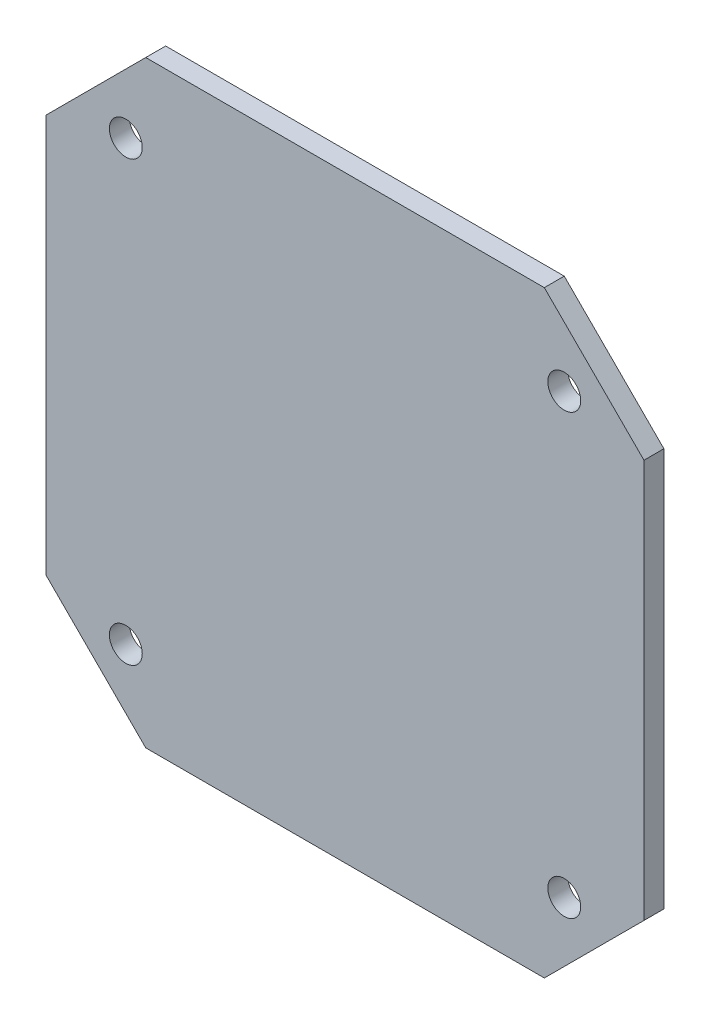
SolidWorks part; units mm, degrees
ref_plane "正面" through (0, 0, 0) normal (0, 0, 1) x (1, 0, 0)
ref_plane "平面" through (0, 0, 0) normal (0, 1, 0) x (1, 0, 0)
ref_plane "右側面" through (0, 0, 0) normal (1, 0, 0) x (0, 0, -1)
sketch "ｽｹｯﾁ1" plane through (0, 0, 0) normal (0, 0, 1) x (1, 0, 0)
  line L1 (-30, 30) -> (30, 30)
  line L2 (-30, 30) -> (-30, -30)
  line L3 (-30, -30) -> (30, -30)
  line L4 (30, 30) -> (30, -30)
  line L5 (-30, 30) -> (30, -30) construction
  line L6 (-30, -30) -> (30, 30) construction
  point P0 (0, 0)
  dimension "D1" = 60
  dimension "D2" = 60
extrude "ﾎﾞｽ - 押し出し1" add sketch "ｽｹｯﾁ1" along normal blind 2
sketch "ｽｹｯﾁ2" plane through (0, 0, 0) normal (0, 0, -1) x (-1, 0, 0)
  line L1 (-30, 30) -> (-22, 30)
  line L2 (-30, 30) -> (-30, 22)
  line L3 (-30, 22) -> (-22, 22)
  line L4 (-22, 30) -> (-22, 22)
  line L5 (-30, -30) -> (-22, -30)
  line L6 (-30, -30) -> (-30, -22)
  line L7 (-30, -22) -> (-22, -22)
  line L8 (-22, -30) -> (-22, -22)
  line L9 (30, -30) -> (22, -30)
  line L10 (30, -30) -> (30, -22)
  line L11 (30, -22) -> (22, -22)
  line L12 (22, -30) -> (22, -22)
  line L13 (30, 30) -> (22, 30)
  line L14 (30, 30) -> (30, 22)
  line L15 (30, 22) -> (22, 22)
  line L16 (22, 30) -> (22, 22)
  circle A0 centre (-22, 22) radius 3.1896
  circle A1 centre (-22, -22) radius 4.7105
  circle A2 centre (22, 22) radius 4.1571
  circle A3 centre (22, -22) radius 4.6505
  dimension "D1" = 8
  dimension "D2" = 8
  dimension "D3" = 8
  dimension "D4" = 8
  dimension "D5" = 8
  dimension "D6" = 8
  dimension "D7" = 8
  dimension "D8" = 8
hole_wizard "M4x0.7 ねじ穴1" positions "3Dｽｹｯﾁ1" profile "ｽｹｯﾁ3" tap size "M4x0.7" standard "JIS"
sketch3d "3Dｽｹｯﾁ1"
  point P0 (22, 22, 0)
  point P3 (22, -22, 0)
  point P6 (-22, -22, 0)
  point P9 (-22, 22, 0)
sketch "ｽｹｯﾁ3" plane through (22, 22, 0) normal (1, 0, 0) x (0, 1, 0)
  line L0 (0, 0) -> (0, 12.4914)
  line L1 (0, 12.4914) -> (1.65, 11.5)
  line L2 (1.65, 11.5) -> (1.65, 0)
  line L5 (1.65, 0) -> (0, 0)
  line L10 (0, 12.4914) -> (-1.65, 11.5) construction
  line L11 (0, -6.35) -> (0, 107.95) construction
  dimension "ねじ下穴ﾄﾞﾘﾙ直径" = 3.3
  dimension "ねじ下穴ﾄﾞﾘﾙの深さ" = 11.5
  dimension "ﾄﾞﾘﾙ角度" = 118
cosmetic thread "穴のねじ山1" parameters "D1"=2, "D2"=4
cosmetic thread "穴のねじ山2" parameters "D1"=2, "D2"=4
cosmetic thread "穴のねじ山3" parameters "D1"=2, "D2"=4
cosmetic thread "穴のねじ山4" parameters "D1"=2, "D2"=4
sketch "ｽｹｯﾁ4" plane through (0, 0, 0) normal (0, 0, -1) x (-1, 0, 0)
  line L0 (-30, -30) -> (-30, -20)
  line L1 (-30, -20) -> (-20, -30)
  line L2 (-24.9986, 25.0014) -> (-30, 20)
  line L3 (-30, -30) -> (-30, 30) construction
  line L4 (-24.9986, 25.0014) -> (-20, 30)
  line L5 (-30, 30) -> (30, 30) construction
  line L6 (-20, 30) -> (-30, 30)
  line L7 (-30, 30) -> (-30, 20)
  line L8 (30, -30) -> (-30, -30) construction
  line L9 (-20, -30) -> (-30, -30)
  line L10 (30, 30) -> (20, 30)
  line L11 (20, 30) -> (30, 20)
  line L12 (30, 30) -> (30, -30) construction
  line L13 (30, 20) -> (30, 30)
  line L14 (30, -30) -> (30, -20)
  line L15 (30, -20) -> (20, -30)
  line L16 (20, -30) -> (30, -30)
  dimension "D1" = 10
  dimension "D2" = 10
  dimension "D3" = 10
  dimension "D4" = 10
  dimension "D5" = 10
  dimension "D6" = 10
  dimension "D7" = 10
  dimension "D8" = 10
extrude "ｶｯﾄ - 押し出し1" cut sketch "ｽｹｯﾁ4" against normal blind 80
